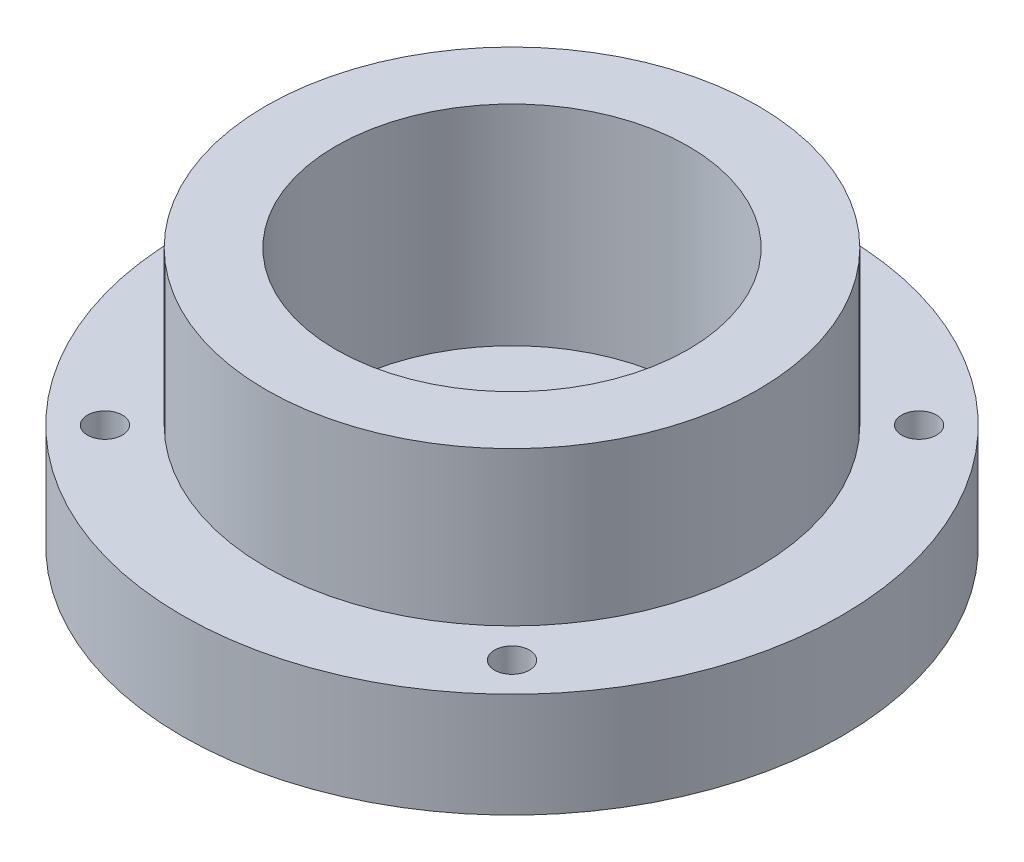
SolidWorks part; units mm, degrees
ref_plane "Front Plane" through (0, 0, 0) normal (0, 0, 1) x (1, 0, 0)
ref_plane "Top Plane" through (0, 0, 0) normal (0, 1, 0) x (1, 0, 0)
ref_plane "Right Plane" through (0, 0, 0) normal (1, 0, 0) x (0, 0, -1)
sketch "Sketch1" plane through (0, 0, 0) normal (0, 1, 0) x (1, 0, 0)
  circle A0 centre (0, 0) radius 35.25
  circle A1 centre (0, 0) radius 15.5
  dimension "D1" = 70.5
  dimension "D2" = 31
extrude "Boss-Extrude1" add sketch "Sketch1" along normal blind 7
sketch "Sketch2" plane through (0, 7, 0) normal (0, 1, 0) x (1, 0, 0)
  circle A0 centre (0, 0) radius 35.25 construction
  circle A1 centre (0, 0) radius 35.25
  circle A2 centre (0, 0) radius 25.25
  dimension "D1" = 50.5
extrude "Boss-Extrude2" add sketch "Sketch2" along normal blind 30
sketch "Sketch3" plane through (0, 7, 0) normal (0, 1, 0) x (1, 0, 0)
  line L0 (0, 0) -> (0, 34.3828) construction
  circle A0 centre (0, 0) radius 20 construction
  circle A1 centre (0, 20) radius 2.5
  circle A2 centre (20, 0) radius 2.5
  circle A3 centre (0, -20) radius 2.5
  circle A4 centre (-20, 0) radius 2.5
  point P15 (0, 0)
  dimension "D1" = 40
  dimension "D2" = 5
  dimension "D3" = 4
extrude "Cut-Extrude1" cut sketch "Sketch3" against normal blind 7
sketch "Sketch4" plane through (0, 0, 0) normal (0, -1, 0) x (1, 0, 0)
  circle A0 centre (0, 0) radius 35.25 construction
  circle A1 centre (0, 0) radius 35.25
  circle A2 centre (0, 0) radius 47.25
  dimension "D1" = 94.5
extrude "Boss-Extrude3" add sketch "Sketch4" against normal blind 15
sketch "Sketch5" plane through (0, 0, 0) normal (0, -1, 0) x (1, 0, 0)
  line L0 (0, 0) -> (0, 44.5449) construction
  line L1 (0, 0) -> (45.4682, 45.4682) construction
  circle A0 centre (0, 0) radius 41.25 construction
  circle A1 centre (29.1682, 29.1682) radius 2.5
  circle A2 centre (29.1682, -29.1682) radius 2.5
  circle A3 centre (-29.1682, -29.1682) radius 2.5
  circle A4 centre (-29.1682, 29.1682) radius 2.5
  point P16 (0, 0)
  dimension "D2" = 82.5
  dimension "D3" = 5
  dimension "D1" = 45
  dimension "D4" = 4
extrude "Cut-Extrude2" cut sketch "Sketch5" against normal blind 15
